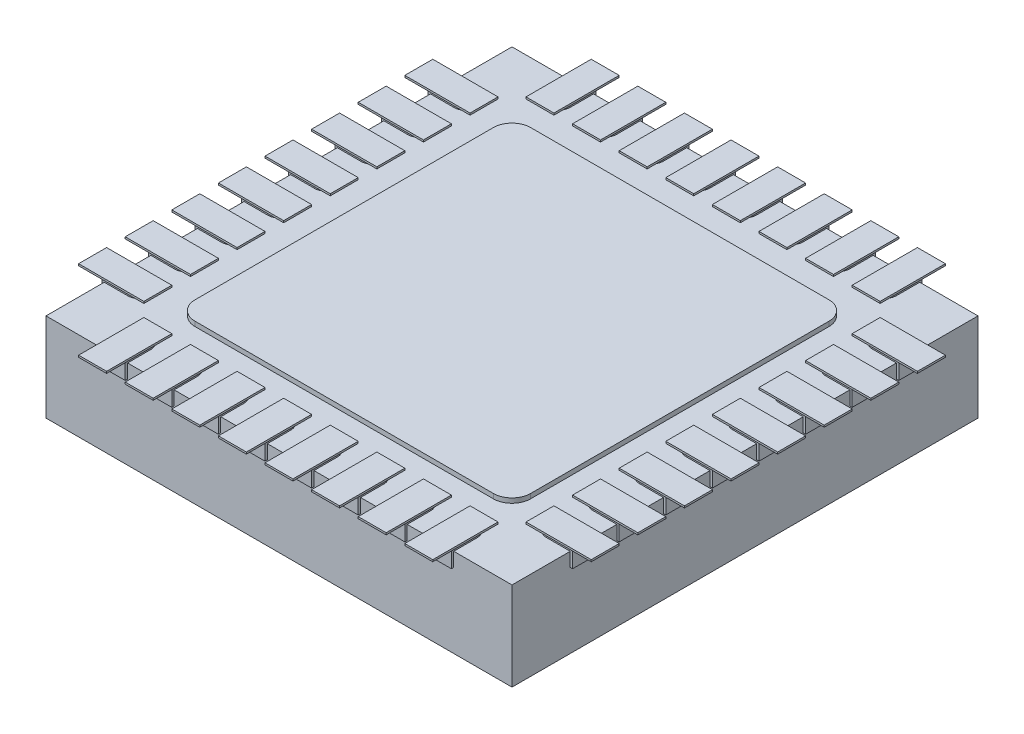
SolidWorks part; units mm, degrees
ref_plane "Front Plane" through (0, 0, 0) normal (0, 0, 1) x (1, 0, 0)
ref_plane "Top Plane" through (0, 0, 0) normal (0, 1, 0) x (1, 0, 0)
ref_plane "Right Plane" through (0, 0, 0) normal (1, 0, 0) x (0, 0, -1)
sketch "Sketch1" plane through (0, 0, 0) normal (0, 1, 0) x (1, 0, 0)
  line L0 (0, -2.75) -> (0, 2.75) construction
  line L1 (-2.525, 2.525) -> (2.525, 2.525)
  line L2 (-2.525, 2.525) -> (-2.525, -2.525)
  line L3 (-2.525, -2.525) -> (2.525, -2.525)
  line L4 (2.525, 2.525) -> (2.525, -2.525)
  line L5 (-2.75, 0) -> (2.75, 0) construction
  dimension "D1" = 5.05
  dimension "D2" = 2.525
  dimension "D3" = 2.525
sketch "Sketch2" plane through (0, 0, 0) normal (0, 1, 0) x (1, 0, 0)
  line L0 (0, -2.75) -> (0, 2.75) construction
  line L1 (-1.6, -1.8) -> (1.6, -1.8)
  line L2 (-1.8, -1.6) -> (-1.8, 1.6)
  line L3 (-1.6, 1.8) -> (1.6, 1.8)
  line L4 (1.8, -1.6) -> (1.8, 1.6)
  line L5 (-2.75, 0) -> (2.75, 0) construction
  line L6 (-1.875, -2.25) -> (-1.875, -2.525)
  line L8 (-1.875, -2.525) -> (-1.625, -2.525)
  line L9 (-1.625, -2.525) -> (-1.625, -2.25)
  line L10 (-1.875, 2.25) -> (-1.875, 2.525)
  line L12 (-1.875, 2.525) -> (-1.625, 2.525)
  line L13 (-1.625, 2.525) -> (-1.625, 2.25)
  line L14 (-1.375, -2.25) -> (-1.375, -2.525)
  line L15 (-1.125, -2.525) -> (-1.125, -2.25)
  line L16 (-1.375, -2.525) -> (-1.125, -2.525)
  line L17 (-1.125, 2.525) -> (-1.125, 2.25)
  line L18 (-1.375, 2.25) -> (-1.375, 2.525)
  line L19 (-1.375, 2.525) -> (-1.125, 2.525)
  line L20 (-0.875, -2.25) -> (-0.875, -2.525)
  line L21 (-0.625, -2.525) -> (-0.625, -2.25)
  line L22 (-0.875, -2.525) -> (-0.625, -2.525)
  line L23 (-0.625, 2.525) -> (-0.625, 2.25)
  line L24 (-0.875, 2.25) -> (-0.875, 2.525)
  line L25 (-0.875, 2.525) -> (-0.625, 2.525)
  line L26 (-0.375, -2.25) -> (-0.375, -2.525)
  line L27 (-0.125, -2.525) -> (-0.125, -2.25)
  line L28 (-0.375, -2.525) -> (-0.125, -2.525)
  line L29 (-0.125, 2.525) -> (-0.125, 2.25)
  line L30 (-0.375, 2.25) -> (-0.375, 2.525)
  line L31 (-0.375, 2.525) -> (-0.125, 2.525)
  line L32 (0.125, -2.25) -> (0.125, -2.525)
  line L33 (0.375, -2.525) -> (0.375, -2.25)
  line L34 (0.125, -2.525) -> (0.375, -2.525)
  line L35 (0.375, 2.525) -> (0.375, 2.25)
  line L36 (0.125, 2.25) -> (0.125, 2.525)
  line L37 (0.125, 2.525) -> (0.375, 2.525)
  line L38 (0.625, -2.25) -> (0.625, -2.525)
  line L39 (0.875, -2.525) -> (0.875, -2.25)
  line L40 (0.625, -2.525) -> (0.875, -2.525)
  line L41 (0.875, 2.525) -> (0.875, 2.25)
  line L42 (0.625, 2.25) -> (0.625, 2.525)
  line L43 (0.625, 2.525) -> (0.875, 2.525)
  line L44 (1.125, -2.25) -> (1.125, -2.525)
  line L45 (1.375, -2.525) -> (1.375, -2.25)
  line L46 (1.125, -2.525) -> (1.375, -2.525)
  line L47 (1.375, 2.525) -> (1.375, 2.25)
  line L48 (1.125, 2.25) -> (1.125, 2.525)
  line L49 (1.125, 2.525) -> (1.375, 2.525)
  line L50 (1.625, -2.25) -> (1.625, -2.525)
  line L51 (1.875, -2.525) -> (1.875, -2.25)
  line L52 (1.625, -2.525) -> (1.875, -2.525)
  line L53 (1.875, 2.525) -> (1.875, 2.25)
  line L54 (1.625, 2.25) -> (1.625, 2.525)
  line L55 (1.625, 2.525) -> (1.875, 2.525)
  line L56 (-2.525, -1.875) -> (-2.245, -1.875)
  line L59 (-2.245, -1.625) -> (-2.525, -1.625)
  line L60 (2.245, -1.875) -> (2.525, -1.875)
  line L62 (2.525, -1.875) -> (2.525, -1.625)
  line L63 (2.525, -1.625) -> (2.245, -1.625)
  line L64 (-2.525, -1.625) -> (-2.525, -1.875)
  line L65 (-2.245, -1.125) -> (-2.525, -1.125)
  line L66 (-2.525, -1.375) -> (-2.245, -1.375)
  line L67 (-2.525, -1.125) -> (-2.525, -1.375)
  line L68 (2.245, -1.375) -> (2.525, -1.375)
  line L69 (2.525, -1.375) -> (2.525, -1.125)
  line L70 (2.525, -1.125) -> (2.245, -1.125)
  line L71 (-2.245, -0.625) -> (-2.525, -0.625)
  line L72 (-2.525, -0.875) -> (-2.245, -0.875)
  line L73 (-2.525, -0.625) -> (-2.525, -0.875)
  line L74 (2.245, -0.875) -> (2.525, -0.875)
  line L75 (2.525, -0.875) -> (2.525, -0.625)
  line L76 (2.525, -0.625) -> (2.245, -0.625)
  line L77 (-2.245, -0.125) -> (-2.525, -0.125)
  line L78 (-2.525, -0.375) -> (-2.245, -0.375)
  line L79 (-2.525, -0.125) -> (-2.525, -0.375)
  line L80 (2.245, -0.375) -> (2.525, -0.375)
  line L81 (2.525, -0.375) -> (2.525, -0.125)
  line L82 (2.525, -0.125) -> (2.245, -0.125)
  line L83 (-2.245, 0.375) -> (-2.525, 0.375)
  line L84 (-2.525, 0.125) -> (-2.245, 0.125)
  line L85 (-2.525, 0.375) -> (-2.525, 0.125)
  line L86 (2.245, 0.125) -> (2.525, 0.125)
  line L87 (2.525, 0.125) -> (2.525, 0.375)
  line L88 (2.525, 0.375) -> (2.245, 0.375)
  line L89 (-2.245, 0.875) -> (-2.525, 0.875)
  line L90 (-2.525, 0.625) -> (-2.245, 0.625)
  line L91 (-2.525, 0.875) -> (-2.525, 0.625)
  line L92 (2.245, 0.625) -> (2.525, 0.625)
  line L93 (2.525, 0.625) -> (2.525, 0.875)
  line L94 (2.525, 0.875) -> (2.245, 0.875)
  line L95 (-2.245, 1.375) -> (-2.525, 1.375)
  line L96 (-2.525, 1.125) -> (-2.245, 1.125)
  line L97 (-2.525, 1.375) -> (-2.525, 1.125)
  line L98 (2.245, 1.125) -> (2.525, 1.125)
  line L99 (2.525, 1.125) -> (2.525, 1.375)
  line L100 (2.525, 1.375) -> (2.245, 1.375)
  line L101 (-2.245, 1.875) -> (-2.525, 1.875)
  line L102 (-2.525, 1.625) -> (-2.245, 1.625)
  line L103 (-2.525, 1.875) -> (-2.525, 1.625)
  line L104 (2.245, 1.625) -> (2.525, 1.625)
  line L105 (2.525, 1.625) -> (2.525, 1.875)
  line L106 (2.525, 1.875) -> (2.245, 1.875)
  line L107 (-2.245, -1.625) -> (-2.245, -1.125) construction
  line L108 (-2.525, 2.525) -> (-2.525, -2.525) construction
  line L109 (-2.525, 2.525) -> (2.525, 2.525) construction
  line L110 (-2.525, -2.525) -> (2.525, -2.525) construction
  line L111 (2.525, 2.525) -> (2.525, -2.525) construction
  arc A0 (1.6, 1.8) -> (1.8, 1.6) centre (1.6, 1.6) cw
  arc A1 (-1.8, 1.6) -> (-1.6, 1.8) centre (-1.6, 1.6) cw
  arc A2 (-1.6, -1.8) -> (-1.8, -1.6) centre (-1.6, -1.6) cw
  arc A3 (1.6, -1.8) -> (1.8, -1.6) centre (1.6, -1.6) ccw
  arc A4 (-1.625, -2.25) -> (-1.875, -2.25) centre (-1.75, -2.25) ccw
  arc A5 (-1.875, 2.25) -> (-1.625, 2.25) centre (-1.75, 2.25) ccw
  arc A6 (-1.125, -2.25) -> (-1.375, -2.25) centre (-1.25, -2.25) ccw
  arc A7 (-1.375, 2.25) -> (-1.125, 2.25) centre (-1.25, 2.25) ccw
  arc A8 (-0.625, -2.25) -> (-0.875, -2.25) centre (-0.75, -2.25) ccw
  arc A9 (-0.875, 2.25) -> (-0.625, 2.25) centre (-0.75, 2.25) ccw
  arc A10 (-0.125, -2.25) -> (-0.375, -2.25) centre (-0.25, -2.25) ccw
  arc A11 (-0.375, 2.25) -> (-0.125, 2.25) centre (-0.25, 2.25) ccw
  arc A12 (0.375, -2.25) -> (0.125, -2.25) centre (0.25, -2.25) ccw
  arc A13 (0.125, 2.25) -> (0.375, 2.25) centre (0.25, 2.25) ccw
  arc A14 (0.875, -2.25) -> (0.625, -2.25) centre (0.75, -2.25) ccw
  arc A15 (0.625, 2.25) -> (0.875, 2.25) centre (0.75, 2.25) ccw
  arc A16 (1.375, -2.25) -> (1.125, -2.25) centre (1.25, -2.25) ccw
  arc A17 (1.125, 2.25) -> (1.375, 2.25) centre (1.25, 2.25) ccw
  arc A18 (1.875, -2.25) -> (1.625, -2.25) centre (1.75, -2.25) ccw
  arc A19 (1.625, 2.25) -> (1.875, 2.25) centre (1.75, 2.25) ccw
  arc A20 (-2.245, -1.875) -> (-2.245, -1.625) centre (-2.245, -1.75) ccw
  arc A21 (2.245, -1.625) -> (2.245, -1.875) centre (2.245, -1.75) ccw
  arc A22 (-2.245, -1.375) -> (-2.245, -1.125) centre (-2.245, -1.25) ccw
  arc A23 (2.245, -1.125) -> (2.245, -1.375) centre (2.245, -1.25) ccw
  arc A24 (-2.245, -0.875) -> (-2.245, -0.625) centre (-2.245, -0.75) ccw
  arc A25 (2.245, -0.625) -> (2.245, -0.875) centre (2.245, -0.75) ccw
  arc A26 (-2.245, -0.375) -> (-2.245, -0.125) centre (-2.245, -0.25) ccw
  arc A27 (2.245, -0.125) -> (2.245, -0.375) centre (2.245, -0.25) ccw
  arc A28 (-2.245, 0.125) -> (-2.245, 0.375) centre (-2.245, 0.25) ccw
  arc A29 (2.245, 0.375) -> (2.245, 0.125) centre (2.245, 0.25) ccw
  arc A30 (-2.245, 0.625) -> (-2.245, 0.875) centre (-2.245, 0.75) ccw
  arc A31 (2.245, 0.875) -> (2.245, 0.625) centre (2.245, 0.75) ccw
  arc A32 (-2.245, 1.125) -> (-2.245, 1.375) centre (-2.245, 1.25) ccw
  arc A33 (2.245, 1.375) -> (2.245, 1.125) centre (2.245, 1.25) ccw
  arc A34 (-2.245, 1.625) -> (-2.245, 1.875) centre (-2.245, 1.75) ccw
  arc A35 (2.245, 1.875) -> (2.245, 1.625) centre (2.245, 1.75) ccw
  point P14 (-1.8, -1.8)
  point P17 (1.8, -1.8)
  dimension "D5" = 0.2
  dimension "D1" = 3.6
  dimension "D2" = 1.8
  dimension "D3" = 1.8
  dimension "D4" = 1.8
  dimension "D6" = 0.25
  dimension "D7" = 0.275
  dimension "D8" = 1.75
  dimension "D10" = 0.5
  dimension "D11" = 1.75
  dimension "D12" = 0.25
  dimension "D13" = 0.28
  dimension "D15" = 0.5
  dimension "D9" = 8
  dimension "D14" = 8
sketch "Sketch3" plane through (0, 0, 0) normal (0, 1, 0) x (1, 0, 0)
  line L0 (0, -2.7775) -> (0, 2.7775) construction
  line L1 (2.5, 2.5) -> (-2.5, 2.5)
  line L2 (2.5, 2.5) -> (2.5, -2.5)
  line L3 (2.5, -2.5) -> (-2.5, -2.5)
  line L4 (-2.5, 2.5) -> (-2.5, -2.5)
  line L5 (-2.7775, 0) -> (2.7775, 0) construction
  dimension "D1" = 5
  dimension "D2" = 2.5
  dimension "D3" = 2.5
  dimension "D4" = 2.5
extrude "Boss-Extrude2" add sketch "Sketch3" against normal blind 0.95
extrude "Boss-Extrude3" add sketch "Sketch2" along normal blind 0.05 and the other way blind 0.15
ref_plane "Plane1" through (0, 0.06, 0) normal (0, 1, 0) x (1, 0, 0)
sketch "Sketch4" plane through (0, 0.06, 0) normal (0, 1, 0) x (1, 0, 0)
  line L0 (-0.5555, 0) -> (0.5555, 0) construction
  line L1 (-1.9, 2.75) -> (-1.6, 2.75)
  line L2 (-1.9, 2.75) -> (-1.9, 2.05)
  line L3 (-1.9, 2.05) -> (-1.6, 2.05)
  line L4 (-1.6, 2.75) -> (-1.6, 2.05)
  line L5 (-1.9, -2.05) -> (-1.6, -2.05)
  line L6 (-1.9, -2.05) -> (-1.9, -2.75)
  line L7 (-1.9, -2.75) -> (-1.6, -2.75)
  line L8 (-1.6, -2.05) -> (-1.6, -2.75)
  line L9 (0, -0.5555) -> (0, 0.5555) construction
  line L10 (-1.4, -2.75) -> (-1.1, -2.75)
  line L11 (-1.1, -2.05) -> (-1.1, -2.75)
  line L12 (-1.4, -2.05) -> (-1.4, -2.75)
  line L13 (-1.4, -2.05) -> (-1.1, -2.05)
  line L14 (-1.4, 2.75) -> (-1.4, 2.05)
  line L15 (-1.4, 2.05) -> (-1.1, 2.05)
  line L16 (-1.1, 2.75) -> (-1.1, 2.05)
  line L17 (-1.4, 2.75) -> (-1.1, 2.75)
  line L18 (-0.9, -2.75) -> (-0.6, -2.75)
  line L19 (-0.6, -2.05) -> (-0.6, -2.75)
  line L20 (-0.9, -2.05) -> (-0.9, -2.75)
  line L21 (-0.9, -2.05) -> (-0.6, -2.05)
  line L22 (-0.9, 2.75) -> (-0.9, 2.05)
  line L23 (-0.9, 2.05) -> (-0.6, 2.05)
  line L24 (-0.6, 2.75) -> (-0.6, 2.05)
  line L25 (-0.9, 2.75) -> (-0.6, 2.75)
  line L26 (-0.4, -2.75) -> (-0.1, -2.75)
  line L27 (-0.1, -2.05) -> (-0.1, -2.75)
  line L28 (-0.4, -2.05) -> (-0.4, -2.75)
  line L29 (-0.4, -2.05) -> (-0.1, -2.05)
  line L30 (-0.4, 2.75) -> (-0.4, 2.05)
  line L31 (-0.4, 2.05) -> (-0.1, 2.05)
  line L32 (-0.1, 2.75) -> (-0.1, 2.05)
  line L33 (-0.4, 2.75) -> (-0.1, 2.75)
  line L34 (0.1, -2.75) -> (0.4, -2.75)
  line L35 (0.4, -2.05) -> (0.4, -2.75)
  line L36 (0.1, -2.05) -> (0.1, -2.75)
  line L37 (0.1, -2.05) -> (0.4, -2.05)
  line L38 (0.1, 2.75) -> (0.1, 2.05)
  line L39 (0.1, 2.05) -> (0.4, 2.05)
  line L40 (0.4, 2.75) -> (0.4, 2.05)
  line L41 (0.1, 2.75) -> (0.4, 2.75)
  line L42 (0.6, -2.75) -> (0.9, -2.75)
  line L43 (0.9, -2.05) -> (0.9, -2.75)
  line L44 (0.6, -2.05) -> (0.6, -2.75)
  line L45 (0.6, -2.05) -> (0.9, -2.05)
  line L46 (0.6, 2.75) -> (0.6, 2.05)
  line L47 (0.6, 2.05) -> (0.9, 2.05)
  line L48 (0.9, 2.75) -> (0.9, 2.05)
  line L49 (0.6, 2.75) -> (0.9, 2.75)
  line L50 (1.1, -2.75) -> (1.4, -2.75)
  line L51 (1.4, -2.05) -> (1.4, -2.75)
  line L52 (1.1, -2.05) -> (1.1, -2.75)
  line L53 (1.1, -2.05) -> (1.4, -2.05)
  line L54 (1.1, 2.75) -> (1.1, 2.05)
  line L55 (1.1, 2.05) -> (1.4, 2.05)
  line L56 (1.4, 2.75) -> (1.4, 2.05)
  line L57 (1.1, 2.75) -> (1.4, 2.75)
  line L58 (1.6, -2.75) -> (1.9, -2.75)
  line L59 (1.9, -2.05) -> (1.9, -2.75)
  line L60 (1.6, -2.05) -> (1.6, -2.75)
  line L61 (1.6, -2.05) -> (1.9, -2.05)
  line L62 (1.6, 2.75) -> (1.6, 2.05)
  line L63 (1.6, 2.05) -> (1.9, 2.05)
  line L64 (1.9, 2.75) -> (1.9, 2.05)
  line L65 (1.6, 2.75) -> (1.9, 2.75)
  line L66 (-1.9, -2.75) -> (-1.4, -2.75) construction
  line L67 (-2.75, 1.1) -> (-2.05, 1.1)
  line L68 (-2.75, 1.9) -> (-2.05, 1.9)
  line L69 (-2.75, 1.9) -> (-2.75, 1.6)
  line L70 (-2.75, 1.6) -> (-2.05, 1.6)
  line L71 (-2.05, 1.9) -> (-2.05, 1.6)
  line L72 (2.05, 1.9) -> (2.75, 1.9)
  line L73 (2.05, 1.9) -> (2.05, 1.6)
  line L74 (2.05, 1.6) -> (2.75, 1.6)
  line L75 (2.75, 1.9) -> (2.75, 1.6)
  line L76 (-2.05, 1.4) -> (-2.05, 1.1)
  line L77 (-2.75, 1.4) -> (-2.05, 1.4)
  line L78 (-2.75, 1.4) -> (-2.75, 1.1)
  line L79 (2.05, 1.4) -> (2.75, 1.4)
  line L80 (2.75, 1.4) -> (2.75, 1.1)
  line L81 (2.05, 1.1) -> (2.75, 1.1)
  line L82 (2.05, 1.4) -> (2.05, 1.1)
  line L83 (-2.75, 0.6) -> (-2.05, 0.6)
  line L84 (-2.05, 0.9) -> (-2.05, 0.6)
  line L85 (-2.75, 0.9) -> (-2.05, 0.9)
  line L86 (-2.75, 0.9) -> (-2.75, 0.6)
  line L87 (2.05, 0.9) -> (2.75, 0.9)
  line L88 (2.75, 0.9) -> (2.75, 0.6)
  line L89 (2.05, 0.6) -> (2.75, 0.6)
  line L90 (2.05, 0.9) -> (2.05, 0.6)
  line L91 (-2.75, 0.1) -> (-2.05, 0.1)
  line L92 (-2.05, 0.4) -> (-2.05, 0.1)
  line L93 (-2.75, 0.4) -> (-2.05, 0.4)
  line L94 (-2.75, 0.4) -> (-2.75, 0.1)
  line L95 (2.05, 0.4) -> (2.75, 0.4)
  line L96 (2.75, 0.4) -> (2.75, 0.1)
  line L97 (2.05, 0.1) -> (2.75, 0.1)
  line L98 (2.05, 0.4) -> (2.05, 0.1)
  line L99 (-2.75, -0.4) -> (-2.05, -0.4)
  line L100 (-2.05, -0.1) -> (-2.05, -0.4)
  line L101 (-2.75, -0.1) -> (-2.05, -0.1)
  line L102 (-2.75, -0.1) -> (-2.75, -0.4)
  line L103 (2.05, -0.1) -> (2.75, -0.1)
  line L104 (2.75, -0.1) -> (2.75, -0.4)
  line L105 (2.05, -0.4) -> (2.75, -0.4)
  line L106 (2.05, -0.1) -> (2.05, -0.4)
  line L107 (-2.75, -0.9) -> (-2.05, -0.9)
  line L108 (-2.05, -0.6) -> (-2.05, -0.9)
  line L109 (-2.75, -0.6) -> (-2.05, -0.6)
  line L110 (-2.75, -0.6) -> (-2.75, -0.9)
  line L111 (2.05, -0.6) -> (2.75, -0.6)
  line L112 (2.75, -0.6) -> (2.75, -0.9)
  line L113 (2.05, -0.9) -> (2.75, -0.9)
  line L114 (2.05, -0.6) -> (2.05, -0.9)
  line L115 (-2.75, -1.4) -> (-2.05, -1.4)
  line L116 (-2.05, -1.1) -> (-2.05, -1.4)
  line L117 (-2.75, -1.1) -> (-2.05, -1.1)
  line L118 (-2.75, -1.1) -> (-2.75, -1.4)
  line L119 (2.05, -1.1) -> (2.75, -1.1)
  line L120 (2.75, -1.1) -> (2.75, -1.4)
  line L121 (2.05, -1.4) -> (2.75, -1.4)
  line L122 (2.05, -1.1) -> (2.05, -1.4)
  line L123 (-2.75, -1.9) -> (-2.05, -1.9)
  line L124 (-2.05, -1.6) -> (-2.05, -1.9)
  line L125 (-2.75, -1.6) -> (-2.05, -1.6)
  line L126 (-2.75, -1.6) -> (-2.75, -1.9)
  line L127 (2.05, -1.6) -> (2.75, -1.6)
  line L128 (2.75, -1.6) -> (2.75, -1.9)
  line L129 (2.05, -1.9) -> (2.75, -1.9)
  line L130 (2.05, -1.6) -> (2.05, -1.9)
  line L131 (-2.75, 1.6) -> (-2.75, 1.1) construction
  dimension "D1" = 0.3
  dimension "D2" = 0.7
  dimension "D3" = 5.5
  dimension "D4" = 2.75
  dimension "D5" = 1.9
  dimension "D7" = 0.5
  dimension "D8" = 2.75
  dimension "D9" = 5.5
  dimension "D10" = 1.9
  dimension "D11" = 0.3
  dimension "D12" = 0.7
  dimension "D14" = 0.5
  dimension "D6" = 8
  dimension "D13" = 8
extrude "Boss-Extrude4" add sketch "Sketch4" against normal blind 0.02
sketch "Sketch5" plane through (0, -0.95, 0) normal (0, -1, 0) x (1, 0, 0)
  line L0 (-1.0975, -0.97) -> (-0.81, -0.97)
  line L1 (1.2, -0.925) -> (-1.0725, -0.925)
  line L2 (-0.9755, -0.75) -> (-1.0725, -0.925)
  line L3 (-0.76, -1.155) -> (-0.495, -1.155)
  line L4 (-1.2, -1.155) -> (-1, -1.155)
  line L5 (-0.76, -1.2) -> (-0.495, -1.2)
  line L6 (-0.76, -1.385) -> (-0.495, -1.385)
  line L7 (-0.76, -1.43) -> (-0.495, -1.43)
  line L8 (-1.2, -1.67) -> (0.42, -1.67)
  line L9 (-1.2, -1.88) -> (0.6956, -1.88)
  line L10 (1.2, -0.97) -> (0.8425, -1.615)
  line L11 (-0.2, -1.615) -> (0.37, -1.615)
  line L12 (0.91, -0.97) -> (0.91, -1.045)
  line L13 (-0.9755, -0.75) -> (1.2, -0.75)
  line L14 (1.2, -0.75) -> (1.2, -0.925)
  line L15 (0.91, -1.045) -> (0.965, -1.045)
  line L16 (0.965, -1.045) -> (0.86, -1.2344)
  line L17 (0.86, -1.2344) -> (0.86, -0.97)
  line L18 (-0.81, -0.97) -> (-0.81, -1.615)
  line L19 (-0.76, -0.97) -> (-0.76, -1.615)
  line L20 (-0.35, -0.97) -> (-0.35, -1.615)
  line L21 (-0.3, -0.97) -> (-0.3, -1.515)
  line L22 (-0.11, -0.97) -> (-0.11, -1.515)
  line L23 (-0.06, -0.97) -> (-0.06, -1.545)
  line L24 (0.13, -0.97) -> (0.13, -1.535)
  line L25 (0.18, -0.97) -> (0.18, -1.535)
  line L26 (0.37, -0.97) -> (0.37, -1.615)
  line L27 (0.42, -0.97) -> (0.42, -1.67)
  line L28 (0.62, -0.97) -> (0.62, -1.67)
  line L29 (0.67, -0.97) -> (0.67, -1.615)
  line L30 (0.17, -1.545) -> (0.14, -1.545)
  line L31 (-0.06, -1.545) -> (-0.08, -1.545)
  line L32 (-0.35, -1.615) -> (-0.76, -1.615)
  line L33 (-1, -1.155) -> (-1, -1.615)
  line L34 (-1.0975, -0.97) -> (-1.2, -1.155)
  line L35 (-0.48, -1.17) -> (-0.48, -1.185)
  line L36 (0.67, -1.615) -> (0.8425, -1.615)
  line L37 (0.62, -1.67) -> (0.812, -1.67)
  line L38 (-0.76, -0.97) -> (-0.35, -0.97)
  line L39 (-0.3, -0.97) -> (-0.11, -0.97)
  line L40 (-0.48, -1.4) -> (-0.48, -1.415)
  line L41 (-0.81, -1.615) -> (-1, -1.615)
  line L42 (-1.2, -1.67) -> (-1.2, -1.88)
  line L43 (0.812, -1.67) -> (0.6956, -1.88)
  line L44 (-0.06, -0.97) -> (0.13, -0.97)
  line L45 (0.18, -0.97) -> (0.37, -0.97)
  line L46 (0.42, -0.97) -> (0.62, -0.97)
  line L47 (0.67, -0.97) -> (0.86, -0.97)
  line L48 (0.91, -0.97) -> (1.2, -0.97)
  line L49 (0.5555, 0) -> (-0.5555, 0) construction
  line L50 (0, -0.5555) -> (0, 0.5555) construction
  line L51 (2.5, 2.5) -> (2.5, -2.5) construction
  line L52 (-2.5, -2.5) -> (-2.5, 2.5) construction
  arc A0 (-0.2, -1.615) -> (-0.3, -1.515) centre (-0.2, -1.515) cw
  arc A1 (-0.08, -1.545) -> (-0.11, -1.515) centre (-0.08, -1.515) cw
  arc A2 (0.17, -1.545) -> (0.18, -1.535) centre (0.17, -1.535) ccw
  arc A3 (0.13, -1.535) -> (0.14, -1.545) centre (0.14, -1.535) ccw
  arc A4 (-0.495, -1.43) -> (-0.48, -1.415) centre (-0.495, -1.415) ccw
  arc A5 (-0.48, -1.4) -> (-0.495, -1.385) centre (-0.495, -1.4) ccw
  arc A6 (-0.495, -1.2) -> (-0.48, -1.185) centre (-0.495, -1.185) ccw
  arc A7 (-0.48, -1.17) -> (-0.495, -1.155) centre (-0.495, -1.17) ccw
  dimension "D25" = 0.1
  dimension "D26" = 0.03
  dimension "D28" = 0.01
  dimension "D33" = 0.015
  dimension "D1" = 0.045
  dimension "D2" = 0.045
  dimension "D3" = 0.045
  dimension "D4" = 0.055
  dimension "D5" = 61
  dimension "D6" = 0.075
  dimension "D7" = 0.055
  dimension "D8" = 0.185
  dimension "D9" = 0.185
  dimension "D10" = 0.185
  dimension "D11" = 0.21
  dimension "D12" = 0.05
  dimension "D13" = 0.05
  dimension "D14" = 0.05
  dimension "D15" = 0.05
  dimension "D16" = 0.05
  dimension "D17" = 0.05
  dimension "D18" = 0.53
  dimension "D19" = 0.2
  dimension "D20" = 0.19
  dimension "D21" = 0.19
  dimension "D22" = 0.19
  dimension "D23" = 0.41
  dimension "D24" = 2.4
  dimension "D27" = 0.07
  dimension "D29" = 0.19
  dimension "D30" = 0.19
  dimension "D31" = 0.05
  dimension "D32" = 0.28
  dimension "D34" = 0.75
  dimension "D35" = 1.2
  dimension "D36" = 0.175
  dimension "D37" = 1.3
  dimension "D38" = 1.3
sketch "Sketch6" plane through (0, -0.95, 0) normal (0, -1, 0) x (1, 0, 0)
  line L0 (1.3, 0.1) -> (-2.5795, 0.1) construction
  line L1 (1.3, 1.9) -> (-2.5795, 1.9) construction
  line L2 (1.3, 1) -> (-2.5795, 1) construction
  line L3 (0, -0.5555) -> (0, 0.5555) construction
  line L4 (0.5555, 0) -> (-0.5555, 0) construction
  text T0 "MEGA16U2" font "SWRomnd" height 0.55
  text T1 "0928 PH" font "SWRomnd" height 0.55
  text T2 "9F3451" font "SWRomnd" height 0.55
  dimension "D1" = 1.3
  dimension "D2" = 0.1
  dimension "D3" = 0.9
  dimension "D4" = 0.9
extrude "Cut-Extrude1" cut sketch "Sketch6" against normal blind 0.05
extrude "Cut-Extrude2" cut sketch "Sketch5" against normal blind 0.05 contours L41 L18 L0 L34 L4 L33 | A7 L35 A6 L5 L19 L6 A5 L40 A4 L7 L32 L20 L38 L3 | A3 L24 L44 L23 L31 A1 L22 L39 L21 A0 L11 L26 L45 L25 A2 L30 | L14 L13 L2 L1 | L46 L27 L8 L42 L9 L43 L37 L28 | L48 L12 L15 L16 L17 L47 L29 L36 L10
sketch "Sketch7" plane through (0, -0.95, 0) normal (0, -1, 0) x (1, 0, 0)
  line L0 (0, -0.5555) -> (0, 0.5555) construction
  line L1 (0.5555, 0) -> (-0.5555, 0) construction
  circle A0 centre (1.75, -1.75) radius 0.3
  dimension "D1" = 0.6
  dimension "D2" = 1.75
  dimension "D3" = 1.75
extrude "Cut-Extrude3" cut sketch "Sketch7" against normal blind 0.1
equation "\"D2@Sketch1\"=\"D1@Sketch1\"/2"
equation "\"D3@Sketch1\"=\"D1@Sketch1\"/2"
